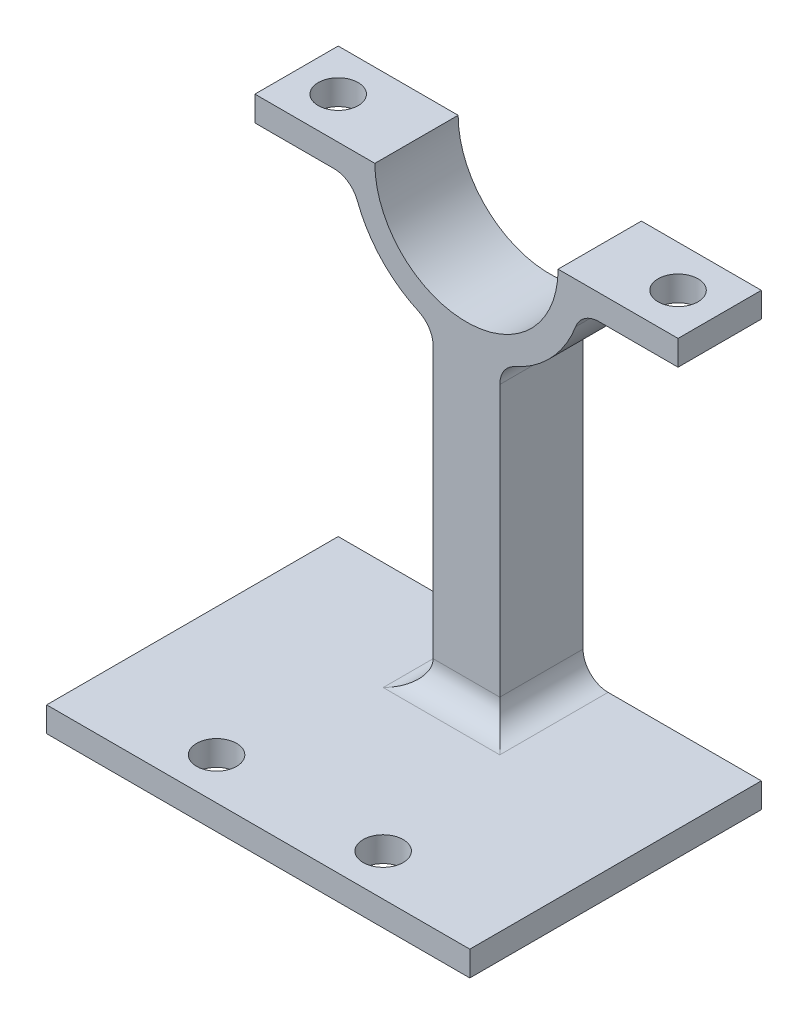
SolidWorks part; units mm, degrees
material "6061-T6 (SS)"
ref_plane "Front Plane" through (0, 0, 0) normal (0, 0, 1) x (1, 0, 0)
ref_plane "Top Plane" through (0, 0, 0) normal (0, 1, 0) x (1, 0, 0)
ref_plane "Right Plane" through (0, 0, 0) normal (1, 0, 0) x (0, 0, -1)
sketch "Sketch1" plane through (0, 0, 0) normal (0, 0, 1) x (1, 0, 0)
  line L0 (5.5, 0) -> (12.7, 0)
  line L1 (12.7, 0) -> (12.7, -1.5)
  line L2 (12.7, -1.5) -> (6.8374, -1.5)
  line L5 (0, 0) -> (0, -7) construction
  line L7 (-12.7, -1.5) -> (-6.8374, -1.5)
  line L8 (-12.7, 0) -> (-12.7, -1.5)
  line L9 (-5.5, 0) -> (-12.7, 0)
  arc A2 (5.5, 0) -> (-5.5, 0) centre (0, 0) cw
  arc A3 (-6.8374, -1.5) -> (6.8374, -1.5) centre (0, 0) ccw
  dimension "D1" = 7
  dimension "D2" = 5.5
  dimension "D3" = 12.7
  dimension "D4" = 1.5
extrude "Boss-Extrude1" add sketch "Sketch1" along normal mid plane 5
sketch "Sketch2" plane through (0, 0, 0) normal (0, 1, 0) x (1, 0, 0)
  line L0 (12.7, 0) -> (-12.7, 0) construction
  line L1 (-12.7, -2.5) -> (-12.7, 2.5) construction
  line L2 (0, 0) -> (0, 2.5) construction
  line L3 (5.5, 2.5) -> (-5.5, 2.5) construction
  circle A0 centre (-10.2, 0) radius 1.2
  circle A1 centre (10.2, 0) radius 1.2
  dimension "D1" = 2.5
  dimension "D2" = 2.4
extrude "Cut-Extrude1" cut sketch "Sketch2" against normal through all
sketch "Sketch6" plane through (0, 0, 0) normal (0, 1, 0) x (1, 0, 0)
  line L0 (-5.5, -2.5) -> (-5.5, 2.5) construction
  line L1 (2, 2.5) -> (-2, 2.5)
  line L2 (2, 2.5) -> (2, -2.5)
  line L3 (2, -2.5) -> (-2, -2.5)
  line L4 (-2, 2.5) -> (-2, -2.5)
  line L5 (2, 2.5) -> (-2, -2.5) construction
  line L6 (2, -2.5) -> (-2, 2.5) construction
  point P0 (0, 0)
  dimension "D1" = 4
extrude "Boss-Extrude2" add sketch "Sketch6" along normal up to surface (18.7918 mm away) from offset 25.5
sketch "Sketch7" plane through (0, -25.5, 0) normal (0, -1, 0) x (1, 0, 0)
  line L0 (0, 0) -> (0, 15) construction
  line L5 (12.7, 2.5) -> (12.7, -2.5) construction
  line L7 (5.5, 2.5) -> (-5.5, 2.5) construction
  line L13 (0, 0) -> (0, -2.5) construction
  line L18 (2, -2.5) -> (-2, -2.5) construction
  line L19 (12.7, -2.5) -> (-12.7, -2.5)
  line L20 (-6.8374, -2.5) -> (-2, -2.5) construction
  line L29 (-12.7, -2.5) -> (-12.7, 15)
  line L30 (-12.7, 15) -> (12.7, 15)
  line L31 (12.7, -2.5) -> (12.7, 15)
  dimension "D1" = 12.5
extrude "Boss-Extrude4" add sketch "Sketch7" along normal blind 1.5
fillet "Fillet1" radius 1.5 7 edges at (2, -25.5, 0) (-2, -25.5, 0) (-6.8374, -1.5, 0) (-2, -6.7082, 0) (2, -6.7082, 0) (6.8374, -1.5, 0) (0, -25.5, 2.5)
sketch "Sketch8" plane through (0, 0, 0) normal (0, 1, 0) x (1, 0, 0)
  line L0 (0, 2.5) -> (0, -15) construction
  line L1 (12.7, -15) -> (-12.7, -15) construction
  line L2 (-5, 2.5) -> (-5, -15) construction
  line L3 (5, 2.5) -> (5, -15) construction
  line L4 (5.5, 2.5) -> (-5.5, 2.5) construction
  line L5 (-5.5, 2.5) -> (-12.7, 2.5) construction
  circle A0 centre (-5, -12.5) radius 1.2
  circle A3 centre (5, -12.5) radius 1.2
  dimension "D2" = 2.4
  dimension "D1" = 2.5
  dimension "D4" = 5
extrude "Cut-Extrude3" cut sketch "Sketch8" against normal through all
